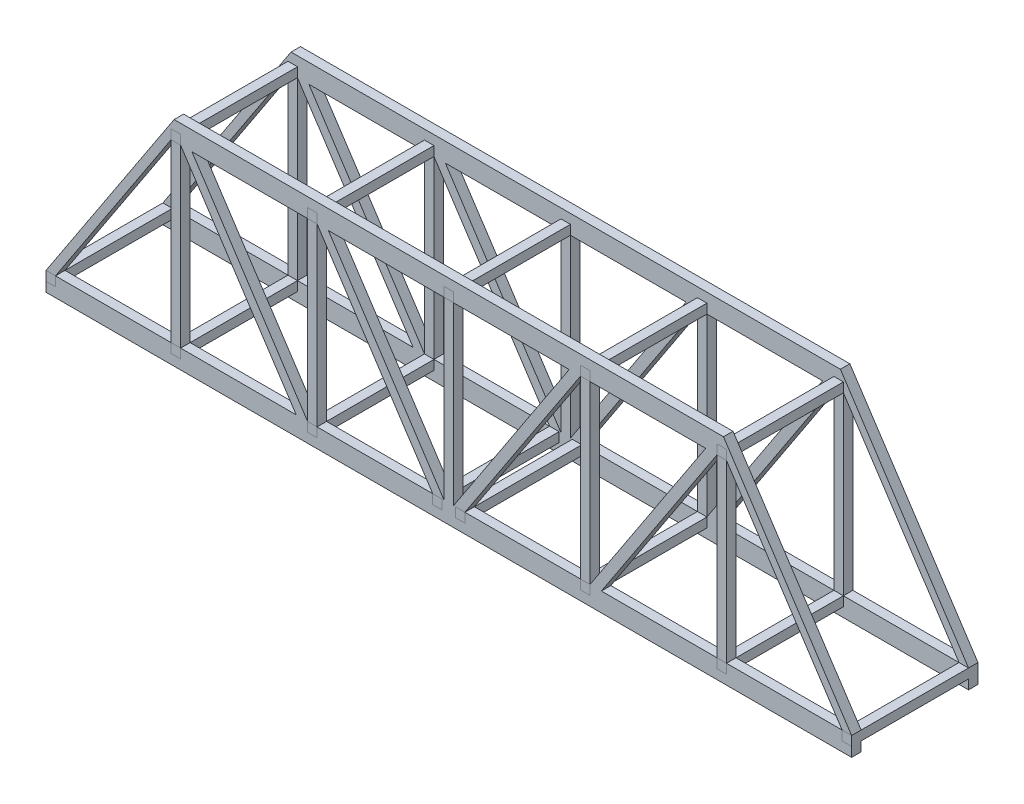
SolidWorks part; units mm, degrees
ref_plane "Front Plane" through (0, 0, 0) normal (0, 0, 1) x (1, 0, 0)
ref_plane "Top Plane" through (0, 0, 0) normal (0, 1, 0) x (1, 0, 0)
ref_plane "Right Plane" through (0, 0, 0) normal (1, 0, 0) x (0, 0, -1)
sketch "Sketch1" plane through (0, 0, 0) normal (0, 0, 1) x (1, 0, 0)
  line L0 (221.1895, 12) -> (221.1895, 123.2464)
  line L2 (-30.8105, 6) -> (-30.8105, 0)
  line L3 (-30.8105, 0) -> (479.1895, 0)
  line L5 (-30.8105, 12) -> (50.2969, 135.2444)
  line L7 (54.401, 12) -> (54.401, 123.2464)
  line L8 (54.401, 123.2464) -> (127.6125, 12)
  line L9 (134.7953, 12) -> (61.5838, 123.2464)
  line L10 (61.5838, 123.2464) -> (134.7953, 123.2464)
  line L11 (134.7953, 123.2464) -> (134.7953, 12)
  line L12 (140.7953, 12) -> (140.7953, 123.2464)
  line L13 (140.7953, 123.2464) -> (214.0068, 12)
  line L14 (221.1895, 12) -> (147.978, 123.2464)
  line L15 (147.978, 123.2464) -> (221.1895, 123.2464)
  line L17 (54.401, 12) -> (127.6125, 12)
  line L18 (-24.8105, 12) -> (48.401, 123.2464)
  line L19 (48.401, 123.2464) -> (48.401, 12)
  line L20 (48.401, 12) -> (-24.8105, 12)
  line L21 (140.7953, 12) -> (214.0068, 12)
  line L22 (224.1895, 0) -> (224.1895, 33.9088) construction
  line L23 (-30.8105, 6) -> (-30.8105, 12)
  line L33 (50.2969, 135.2444) -> (398.0821, 135.2444)
  line L38 (479.1895, 6) -> (479.1895, 12)
  line L40 (307.5838, 12) -> (234.3722, 12)
  line L41 (399.978, 12) -> (473.1895, 12)
  line L42 (399.978, 123.2464) -> (399.978, 12)
  line L43 (473.1895, 12) -> (399.978, 123.2464)
  line L44 (393.978, 12) -> (320.7665, 12)
  line L45 (300.401, 123.2464) -> (227.1895, 123.2464)
  line L46 (227.1895, 12) -> (300.401, 123.2464)
  line L47 (307.5838, 123.2464) -> (234.3722, 12)
  line L48 (307.5838, 12) -> (307.5838, 123.2464)
  line L49 (313.5838, 123.2464) -> (313.5838, 12)
  line L50 (386.7953, 123.2464) -> (313.5838, 123.2464)
  line L51 (313.5838, 12) -> (386.7953, 123.2464)
  line L52 (393.978, 123.2464) -> (320.7665, 12)
  line L53 (393.978, 12) -> (393.978, 123.2464)
  line L54 (479.1895, 12) -> (398.0821, 135.2444)
  line L55 (227.1895, 12) -> (227.1895, 123.2464)
  line L56 (479.1895, 6) -> (479.1895, 0)
  point P24 (224.1895, 135.2444)
  point P42 (0, 0)
  dimension "D2" = 6
  dimension "D3" = 6
  dimension "D5" = 6
  dimension "D7" = 6
  dimension "D12" = 6
  dimension "D19" = 224.1895
extrude "Boss-Extrude1" add sketch "Sketch1" along normal blind 6
sketch "Sketch2" plane through (0, 0, 0) normal (0, 0, -1) x (-1, 0, 0)
  line L0 (-479.1895, 0) -> (-479.1895, 12) construction
  line L1 (-473.1895, 12) -> (-479.1895, 12)
  line L2 (-473.1895, 12) -> (-473.1895, 6)
  line L3 (-473.1895, 6) -> (-479.1895, 6)
  line L4 (-479.1895, 12) -> (-479.1895, 6)
  line L5 (-224.1895, 0) -> (-224.1895, 135.2444) construction
  line L6 (-399.978, 12) -> (-393.978, 12)
  line L7 (-399.978, 12) -> (-399.978, 6)
  line L8 (-399.978, 6) -> (-393.978, 6)
  line L9 (-393.978, 12) -> (-393.978, 6)
  line L10 (-313.5838, 12) -> (-307.5838, 12)
  line L11 (-313.5838, 12) -> (-313.5838, 6)
  line L12 (-313.5838, 6) -> (-307.5838, 6)
  line L13 (-307.5838, 12) -> (-307.5838, 6)
  line L14 (-234.3722, 12) -> (-228.3722, 12)
  line L15 (-234.3722, 12) -> (-234.3722, 6)
  line L16 (-234.3722, 6) -> (-228.3722, 6)
  line L17 (-228.3722, 12) -> (-228.3722, 6)
  line L18 (-399.978, 123.2464) -> (-393.978, 123.2464)
  line L19 (-399.978, 123.2464) -> (-399.978, 129.2464)
  line L20 (-399.978, 129.2464) -> (-393.978, 129.2464)
  line L21 (-393.978, 123.2464) -> (-393.978, 129.2464)
  line L22 (-313.5838, 123.2464) -> (-307.5838, 123.2464)
  line L23 (-313.5838, 123.2464) -> (-313.5838, 129.2464)
  line L24 (-313.5838, 129.2464) -> (-307.5838, 129.2464)
  line L25 (-307.5838, 123.2464) -> (-307.5838, 129.2464)
  line L26 (30.8105, 0) -> (-479.1895, 0) construction
  line L27 (-398.0821, 135.2444) -> (-50.2969, 135.2444) construction
  line L28 (-140.7953, 123.2464) -> (-140.7953, 129.2464)
  line L29 (-134.7953, 129.2464) -> (-140.7953, 129.2464)
  line L30 (-134.7953, 123.2464) -> (-134.7953, 129.2464)
  line L31 (-134.7953, 123.2464) -> (-140.7953, 123.2464)
  line L32 (-54.401, 123.2464) -> (-54.401, 129.2464)
  line L33 (-48.401, 129.2464) -> (-54.401, 129.2464)
  line L34 (-48.401, 123.2464) -> (-48.401, 129.2464)
  line L35 (-48.401, 123.2464) -> (-54.401, 123.2464)
  line L36 (-220.0068, 12) -> (-220.0068, 6)
  line L37 (-214.0068, 6) -> (-220.0068, 6)
  line L38 (-214.0068, 12) -> (-214.0068, 6)
  line L39 (-214.0068, 12) -> (-220.0068, 12)
  line L40 (-140.7953, 12) -> (-140.7953, 6)
  line L41 (-134.7953, 6) -> (-140.7953, 6)
  line L42 (-134.7953, 12) -> (-134.7953, 6)
  line L43 (-134.7953, 12) -> (-140.7953, 12)
  line L44 (-54.401, 12) -> (-54.401, 6)
  line L45 (-48.401, 6) -> (-54.401, 6)
  line L46 (-48.401, 12) -> (-48.401, 6)
  line L47 (-48.401, 12) -> (-54.401, 12)
  line L48 (30.8105, 12) -> (30.8105, 6)
  line L49 (24.8105, 6) -> (30.8105, 6)
  line L50 (24.8105, 12) -> (24.8105, 6)
  line L51 (24.8105, 12) -> (30.8105, 12)
  line L53 (-227.1895, 123.2464) -> (-221.1895, 123.2464)
  line L54 (-227.1895, 123.2464) -> (-227.1895, 129.2464)
  line L55 (-227.1895, 129.2464) -> (-221.1895, 129.2464)
  line L56 (-221.1895, 123.2464) -> (-221.1895, 129.2464)
  dimension "D1" = 6
  dimension "D2" = 6
  dimension "D3" = 6
extrude "Boss-Extrude2" add sketch "Sketch2" against normal blind 40 and the other way blind 0.0001
mirror "Mirror1" about plane through (0, 0, 40) normal (0, 0, 1) of bodies 102
